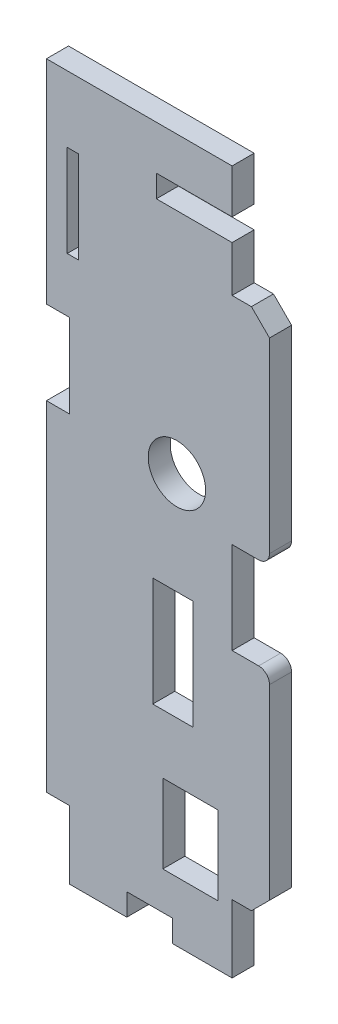
SolidWorks part; units mm, degrees
ref_plane "Front Plane" through (0, 0, 0) normal (0, 0, 1) x (1, 0, 0)
ref_plane "Top Plane" through (0, 0, 0) normal (0, 1, 0) x (1, 0, 0)
ref_plane "Right Plane" through (0, 0, 0) normal (1, 0, 0) x (0, 0, -1)
sketch "Model" plane through (0, 0, 0) normal (0, 0, 1) x (1, 0, 0)
  line L273 (2.8702, 88.011) -> (2.8702, 75.311)
  line L274 (25.654, 91.0844) -> (15.1892, 91.0844)
  line L275 (2.8702, 88.011) -> (4.445, 88.011)
  line L276 (14.6939, 27.305) -> (14.6939, 42.3926)
  line L277 (15.1892, 88.011) -> (15.1892, 91.0844)
  line L278 (15.1892, 88.011) -> (25.654, 88.011)
  line L279 (17.399, 0) -> (25.654, 0)
  line L280 (17.399, 0) -> (17.399, 3.048)
  line L281 (11.0998, 3.048) -> (17.399, 3.048)
  line L282 (11.0998, 0) -> (11.0998, 3.048)
  line L283 (3.175, 0) -> (11.0998, 0)
  line L284 (3.175, 0) -> (3.175, 9.398)
  line L285 (3.175, 9.398) -> (0, 9.398)
  line L286 (0, 9.398) -> (0, 56.261)
  line L287 (0, 56.261) -> (3.175, 56.261)
  line L288 (3.175, 56.261) -> (3.175, 67.818)
  line L289 (0, 67.818) -> (3.175, 67.818)
  line L290 (0, 97.1804) -> (0, 67.818)
  line L291 (25.654, 97.1804) -> (0, 97.1804)
  line L292 (20.2819, 27.305) -> (14.6939, 27.305)
  line L293 (20.2819, 27.305) -> (20.2819, 42.3926)
  line L294 (20.2819, 42.3926) -> (14.6939, 42.3926)
  line L295 (4.445, 75.311) -> (2.8702, 75.311)
  line L296 (4.445, 88.011) -> (4.445, 75.311)
  line L363 (25.654, 91.0844) -> (25.654, 97.1804)
  line L364 (16.0772, 8.2619) -> (23.7372, 8.2619)
  line L365 (23.7372, 8.2619) -> (23.7372, 19.1319)
  line L366 (23.7372, 19.1319) -> (16.0772, 19.1319)
  line L367 (16.0772, 19.1319) -> (16.0772, 8.2619)
  line L480 (25.654, 88.011) -> (25.654, 81.676)
  line L481 (25.654, 51.8695) -> (25.654, 39.1895)
  line L482 (25.654, 9.383) -> (25.654, 0)
  line L483 (25.654, 39.1895) -> (29.324, 39.1895)
  line L484 (28.324, 9.383) -> (25.654, 9.383)
  line L485 (25.654, 81.676) -> (28.324, 81.676)
  line L486 (29.324, 51.8695) -> (25.654, 51.8695)
  line L487 (30.824, 79.176) -> (30.824, 53.3695)
  line L488 (30.824, 37.6895) -> (30.824, 11.883)
  line L509 (28.324, 81.676) -> (30.824, 79.176)
  line L510 (30.824, 11.883) -> (28.324, 9.383)
  circle A61 centre (18.0276, 56.534) radius 3.9654
  arc A70 (29.324, 51.8695) -> (30.824, 53.3695) centre (29.324, 53.3695) ccw
  arc A71 (30.824, 37.6895) -> (29.324, 39.1895) centre (29.324, 37.6895) ccw
extrude "Boss-Extrude1" add sketch "Model" along normal blind 3.048
